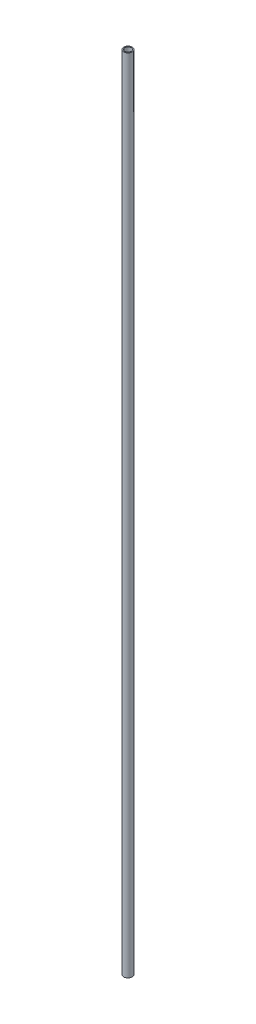
SolidWorks part; units mm, degrees
ref_plane "Front Plane" through (0, 0, 0) normal (0, 0, 1) x (1, 0, 0)
ref_plane "Top Plane" through (0, 0, 0) normal (0, 1, 0) x (1, 0, 0)
ref_plane "Right Plane" through (0, 0, 0) normal (1, 0, 0) x (0, 0, -1)
sketch "Sketch1" plane through (0, 0, 0) normal (0, 1, 0) x (1, 0, 0)
  circle A0 centre (0, 0) radius 7.8994
  circle A1 centre (0, 0) radius 10.668
  dimension "D1" = 15.7988
  dimension "D2" = 21.336
extrude "Boss-Extrude1" add sketch "Sketch1" along normal blind 2000
